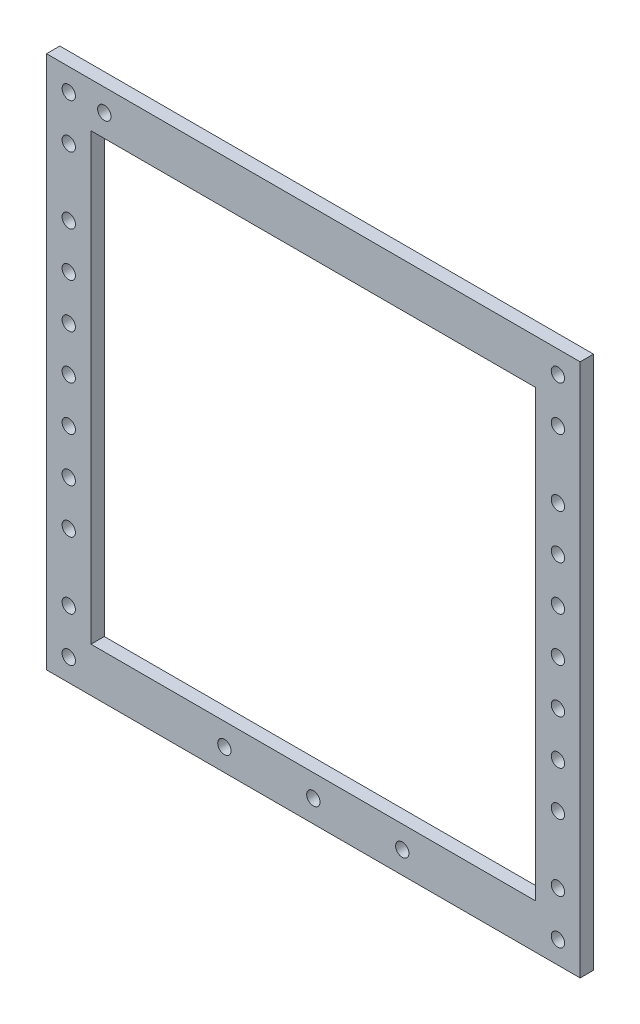
SolidWorks part; units mm, degrees
ref_plane "Plano frontal" through (0, 0, 0) normal (0, 0, 1) x (1, 0, 0)
ref_plane "Plano superior" through (0, 0, 0) normal (0, 1, 0) x (1, 0, 0)
ref_plane "Plano direito" through (0, 0, 0) normal (1, 0, 0) x (0, 0, -1)
sketch "Esboço1" plane through (0, 0, 0) normal (0, 0, 1) x (1, 0, 0)
  line L1 (-6.5269, 6.3462) -> (113.4731, 6.3462)
  line L2 (-6.5269, 6.3462) -> (-6.5269, -113.6538)
  line L3 (-6.5269, -113.6538) -> (113.4731, -113.6538)
  line L4 (113.4731, 6.3462) -> (113.4731, -113.6538)
  dimension "D1" = 120
  dimension "D2" = 120
extrude "Ressalto-extrusão1" add sketch "Esboço1" along normal blind 3
sketch "Esboço2" plane through (0, 0, 3) normal (0, 0, 1) x (1, 0, 0)
  line L0 (-6.5269, 6.3462) -> (-6.5269, -113.6538) construction
  line L1 (3.4731, -103.6538) -> (103.4731, -103.6538)
  line L2 (3.4731, -103.6538) -> (3.4731, -3.6538)
  line L3 (3.4731, -3.6538) -> (103.4731, -3.6538)
  line L4 (103.4731, -103.6538) -> (103.4731, -3.6538)
  line L5 (113.4731, 6.3462) -> (-6.5269, 6.3462) construction
  line L6 (113.4731, -113.6538) -> (113.4731, 6.3462) construction
  line L7 (-6.5269, -113.6538) -> (113.4731, -113.6538) construction
  dimension "D1" = 10
  dimension "D2" = 10
  dimension "D3" = 10
  dimension "D4" = 10
extrude "Corte-extrusão1" cut sketch "Esboço2" against normal through all
sketch "Esboço3" plane through (0, 0, 3) normal (0, 0, 1) x (1, 0, 0)
  line L3 (113.4731, 6.3462) -> (-6.5269, 6.3462) construction
  line L4 (-6.5269, 6.3462) -> (-6.5269, -113.6538) construction
  line L5 (-6.5269, -113.6538) -> (113.4731, -113.6538) construction
  line L6 (53.4731, 6.3462) -> (53.4731, -30.3607) construction
  circle A0 centre (-1.5269, 1.3462) radius 1.5
  circle A1 centre (-1.5269, -108.6538) radius 1.5
  circle A2 centre (-1.5269, -33.6538) radius 1.5
  circle A3 centre (-1.5269, -53.6538) radius 1.5
  circle A4 centre (-1.5269, -73.6538) radius 1.5
  circle A5 centre (108.4731, -73.6538) radius 1.5
  circle A6 centre (108.4731, -53.6538) radius 1.5
  circle A7 centre (108.4731, -33.6538) radius 1.5
  circle A8 centre (108.4731, -108.6538) radius 1.5
  circle A9 centre (108.4731, 1.3462) radius 1.5
  point P16 (-6.5269, -53.6538)
  dimension "D1" = 5
  dimension "D2" = 5
  dimension "D3" = 35
  dimension "D4" = 20
  dimension "D5" = 5
  dimension "D6" = 35
  dimension "D7" = 3
  dimension "D8" = 3
  dimension "D9" = 3
  dimension "D10" = 3
  dimension "D11" = 3
  dimension "D12" = 5
  dimension "D13" = 5
  dimension "D14" = 5
  dimension "D15" = 5
extrude "Corte-extrusão2" cut sketch "Esboço3" against normal through all
sketch "Esboço4" plane through (0, 0, 3) normal (0, 0, 1) x (1, 0, 0)
  line L0 (113.4731, 6.3462) -> (-6.5269, 6.3462) construction
  circle A0 centre (6.4731, 1.3462) radius 1.5
  circle A1 centre (-1.5269, 1.3462) radius 1.5 construction
  dimension "D1" = 3
  dimension "D2" = 5
  dimension "D3" = 8
extrude "Corte-extrusão3" cut sketch "Esboço4" against normal through all
sketch "Esboço5" plane through (0, 0, 3) normal (0, 0, 1) x (1, 0, 0)
  line L1 (-6.5269, -113.6538) -> (113.4731, -113.6538) construction
  circle A0 centre (73.4731, -108.6538) radius 1.5
  circle A1 centre (53.4731, -108.6538) radius 1.5
  circle A2 centre (33.4731, -108.6538) radius 1.5
  circle A3 centre (108.4731, -108.6538) radius 1.5 construction
  circle A4 centre (-1.5269, -108.6538) radius 1.5 construction
  dimension "D1" = 3
  dimension "D2" = 3
  dimension "D3" = 3
  dimension "D4" = 35
  dimension "D5" = 35
  dimension "D6" = 5
  dimension "D7" = 5
  dimension "D8" = 5
  dimension "D9" = 20
extrude "Corte-extrusão4" cut sketch "Esboço5" against normal through all
sketch "Esboço6" plane through (0, 0, 3) normal (0, 0, 1) x (1, 0, 0)
  line L0 (113.4731, -113.6538) -> (113.4731, 6.3462) construction
  line L1 (103.4731, -3.6538) -> (3.4731, -3.6538) construction
  line L2 (3.4731, -103.6538) -> (103.4731, -103.6538) construction
  line L3 (53.4731, -113.6538) -> (53.4731, 6.3462) construction
  line L4 (-6.5269, -113.6538) -> (113.4731, -113.6538) construction
  line L5 (113.4731, 6.3462) -> (-6.5269, 6.3462) construction
  line L6 (103.4731, -103.6538) -> (103.4731, -3.6538) construction
  circle A0 centre (108.4731, -23.6538) radius 1.5
  circle A1 centre (108.4731, -43.6538) radius 1.5
  circle A2 centre (108.4731, -63.6538) radius 1.5
  circle A3 centre (108.4731, -83.6538) radius 1.5
  circle A4 centre (-1.5269, -83.6538) radius 1.5
  circle A5 centre (-1.5269, -63.6538) radius 1.5
  circle A6 centre (-1.5269, -43.6538) radius 1.5
  circle A7 centre (-1.5269, -23.6538) radius 1.5
  circle A8 centre (108.4731, -8.6538) radius 1.5
  circle A9 centre (108.4731, -98.6538) radius 1.5
  circle A10 centre (-1.5269, -98.6538) radius 1.5
  circle A11 centre (-1.5269, -8.6538) radius 1.5
  dimension "D1" = 3
  dimension "D2" = 20
  dimension "D3" = 3
  dimension "D4" = 20
  dimension "D5" = 3
  dimension "D6" = 20
  dimension "D7" = 3
  dimension "D8" = 20
  dimension "D9" = 20
  dimension "D10" = 5
  dimension "D11" = 5
  dimension "D12" = 5
  dimension "D13" = 15
  dimension "D14" = 3
  dimension "D15" = 15
  dimension "D16" = 5
  dimension "D17" = 3
  dimension "D18" = 5
extrude "Corte-extrusão5" cut sketch "Esboço6" against normal through all
